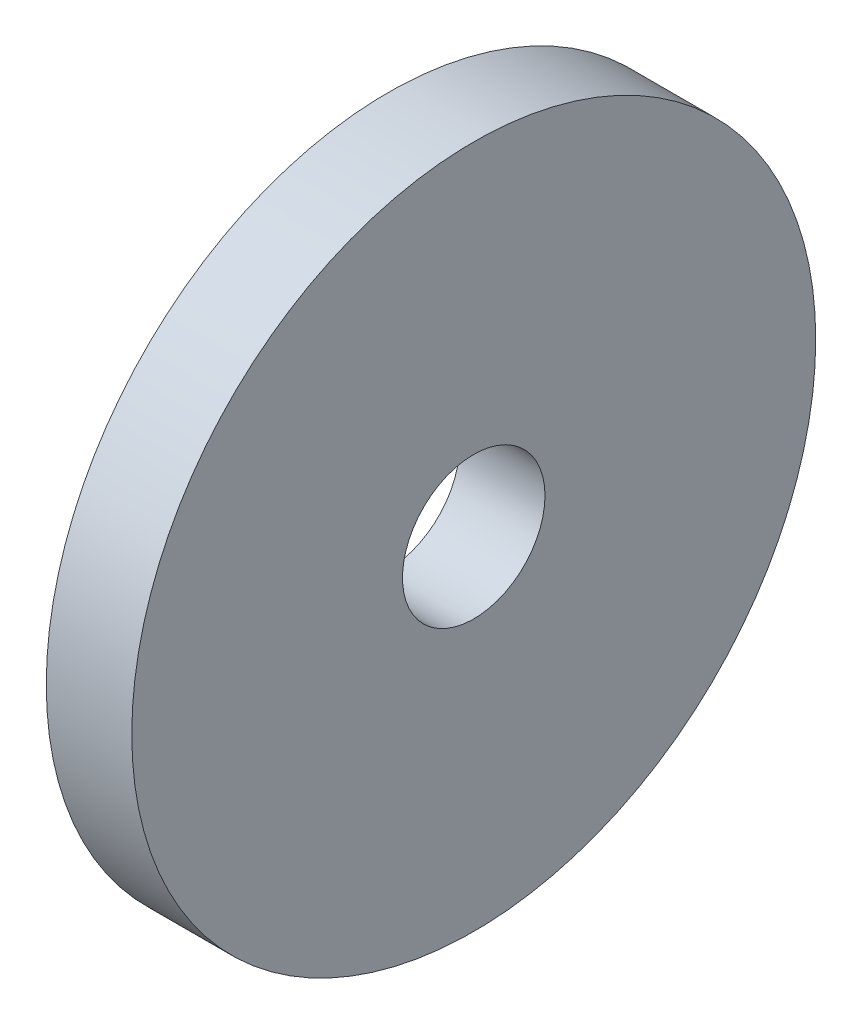
SolidWorks part; units mm, degrees
ref_plane "Front Plane" through (0, 0, 0) normal (0, 0, 1) x (1, 0, 0)
ref_plane "Top Plane" through (0, 0, 0) normal (0, 1, 0) x (1, 0, 0)
ref_plane "Right Plane" through (0, 0, 0) normal (1, 0, 0) x (0, 0, -1)
sketch "Sketch1" plane through (0, 0, 0) normal (1, 0, 0) x (0, 0, -1)
  circle A0 centre (0, 0) radius 12
  dimension "D1" = 24
extrude "gear_body_extrude" add sketch "Sketch1" along normal blind 3
sketch "Sketch2" plane through (3, 0, 0) normal (1, 0, 0) x (0, 0, -1)
  circle A0 centre (0, 0) radius 2.5
  dimension "D1" = 5
extrude "axle_hole" cut sketch "Sketch2" against normal blind 3
